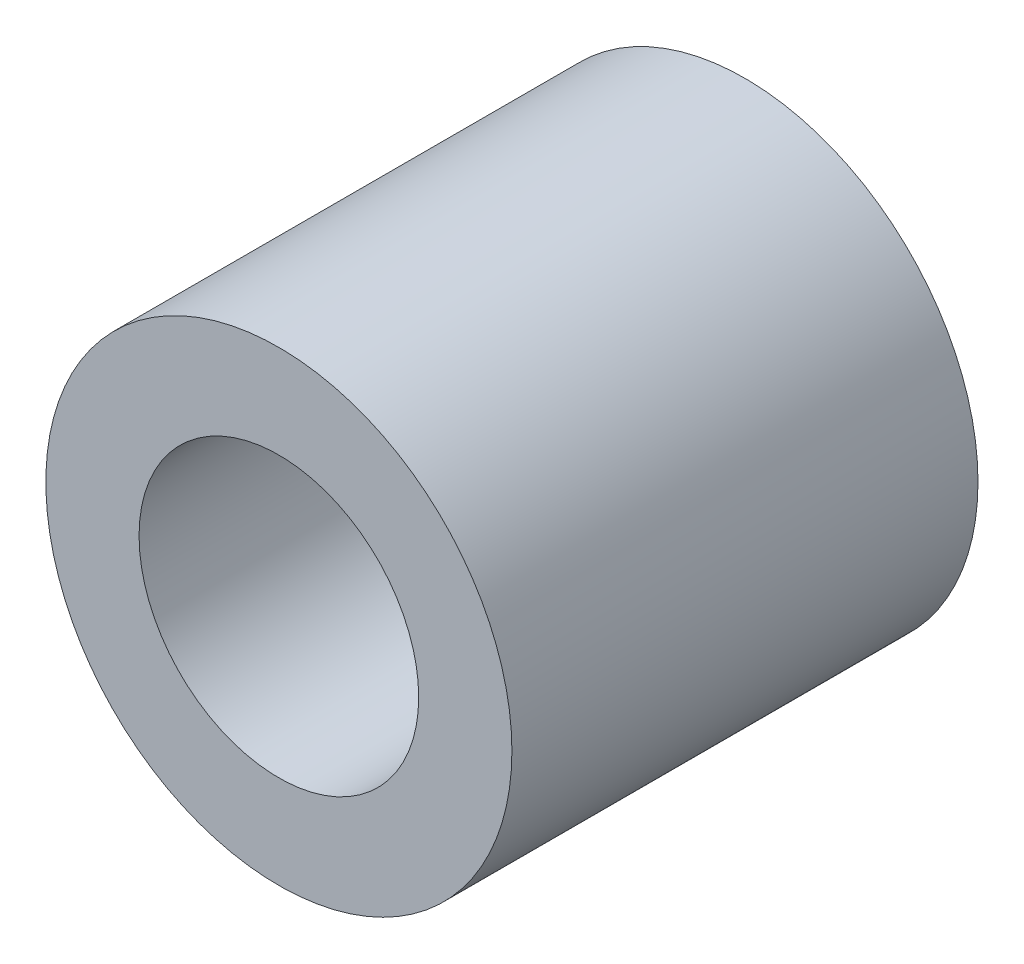
SolidWorks part; units mm, degrees
material "ﾎﾟﾘｵｷｼﾒﾁﾚﾝ(POM)ｱｾﾀｰﾙ共重合体"
ref_plane "Front Plane" through (0, 0, 0) normal (0, 0, 1) x (1, 0, 0)
ref_plane "Top Plane" through (0, 0, 0) normal (0, 1, 0) x (1, 0, 0)
ref_plane "Right Plane" through (0, 0, 0) normal (1, 0, 0) x (0, 0, -1)
sketch "Sketch2" plane through (0, 0, 0) normal (0, 0, 1) x (1, 0, 0)
  circle A0 centre (0, 0) radius 2.5
  circle A1 centre (0, 0) radius 1.5
  dimension "D1" = 3
  dimension "D2" = 5
  dimension "D3" = 5
extrude "Boss-Extrude1" add sketch "Sketch2" along normal blind 5
